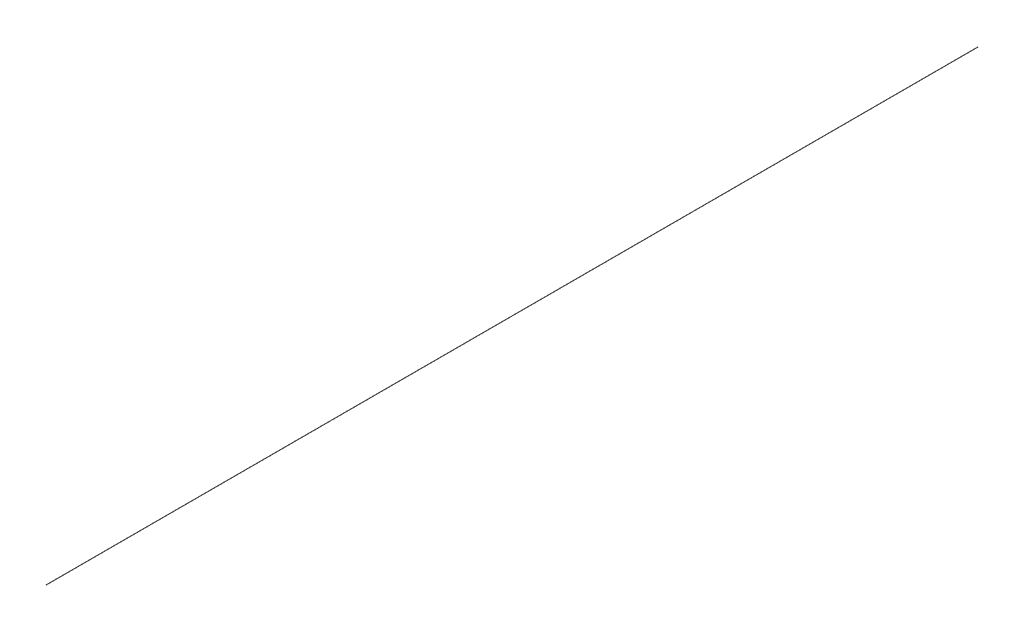
SolidWorks part; units mm, degrees
ref_plane "Front Plane" through (0, 0, 0) normal (0, 0, 1) x (1, 0, 0)
ref_plane "Top Plane" through (0, 0, 0) normal (0, 1, 0) x (1, 0, 0)
ref_plane "Right Plane" through (0, 0, 0) normal (1, 0, 0) x (0, 0, -1)
sketch "Sketch1" plane through (0, 0, 0) normal (0, 0, 1) x (1, 0, 0)
  circle A0 centre (0, 0) radius 3.175
  dimension "D1" = 6.35
extrude "Boss-Extrude1" add sketch "Sketch1" against normal blind 26193.8
